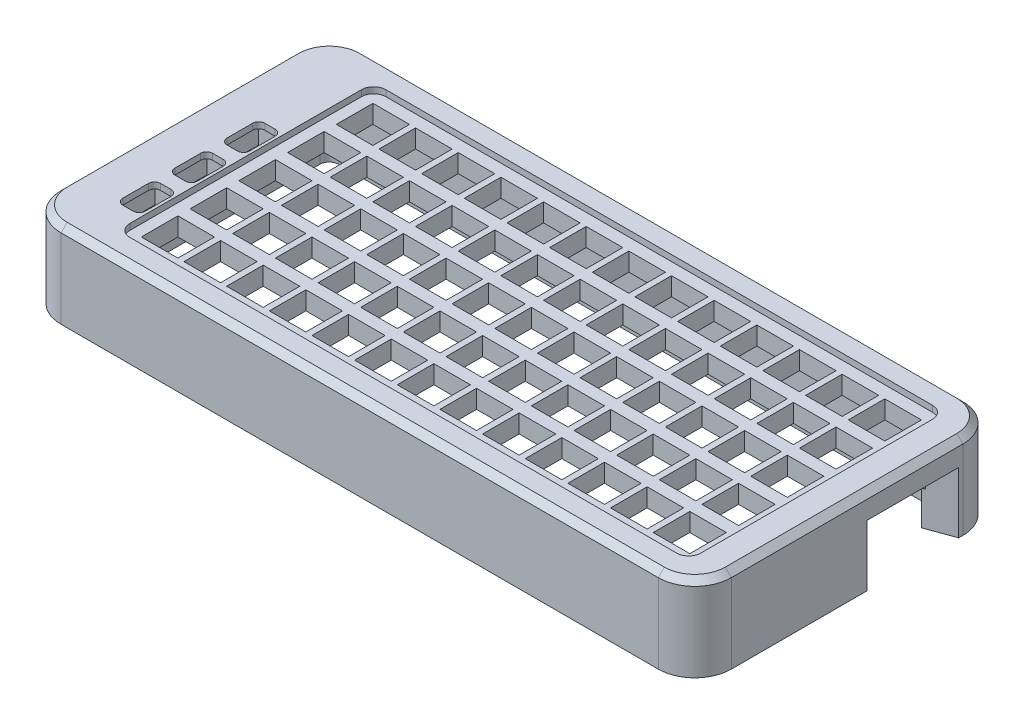
SolidWorks part; units mm, degrees
ref_plane "前视基准面" through (0, 0, 0) normal (0, 0, 1) x (1, 0, 0)
ref_plane "上视基准面" through (0, 0, 0) normal (0, 1, 0) x (1, 0, 0)
ref_plane "右视基准面" through (0, 0, 0) normal (1, 0, 0) x (0, 0, -1)
other "Configuration Table"
sketch "草图1" plane through (0, 0, 0) normal (0, 1, 0) x (1, 0, 0)
  line L1 (-55, -25) -> (55, -25)
  line L2 (-55, -25) -> (-55, 25)
  line L3 (-55, 25) -> (55, 25)
  line L4 (55, -25) -> (55, 25)
  line L5 (-55, -25) -> (55, 25) construction
  line L6 (-55, 25) -> (55, -25) construction
  point P0 (0, 0)
  dimension "D1" = 50
  dimension "D2" = 110
extrude "凸台-拉伸1" add sketch "草图1" along normal blind 3
sketch "草图2" plane through (0, 0, 0) normal (0, -1, 0) x (1, 0, 0)
  line L0 (46.3251, 14.2) -> (44.0251, 17.8) construction
  line L1 (48.1751, 11) -> (48.1751, 5)
  line L2 (48.1751, 19) -> (42.1751, 19)
  line L3 (48.1751, 19) -> (48.1751, 13)
  line L4 (48.1751, 13) -> (42.1751, 13)
  line L5 (42.1751, 19) -> (42.1751, 13)
  line L6 (48.1751, 19) -> (42.1751, 13) construction
  line L7 (48.1751, 13) -> (42.1751, 19) construction
  line L8 (48.1751, 5) -> (42.1751, 5)
  line L9 (42.1751, 11) -> (42.1751, 5)
  line L10 (48.1751, 11) -> (42.1751, 11)
  line L11 (48.1751, 3) -> (48.1751, -3)
  line L12 (48.1751, -3) -> (42.1751, -3)
  line L13 (42.1751, 3) -> (42.1751, -3)
  line L14 (48.1751, 3) -> (42.1751, 3)
  line L15 (48.1751, -5) -> (48.1751, -11)
  line L16 (48.1751, -11) -> (42.1751, -11)
  line L17 (42.1751, -5) -> (42.1751, -11)
  line L18 (48.1751, -5) -> (42.1751, -5)
  line L19 (48.1751, -13) -> (48.1751, -19)
  line L20 (48.1751, -19) -> (42.1751, -19)
  line L21 (42.1751, -13) -> (42.1751, -19)
  line L22 (48.1751, -13) -> (42.1751, -13)
  line L23 (41.1751, 11) -> (41.1751, 5)
  line L24 (41.1751, 5) -> (35.1751, 5)
  line L25 (35.1751, 11) -> (35.1751, 5)
  line L26 (41.1751, 11) -> (35.1751, 11)
  line L27 (41.1751, 3) -> (41.1751, -3)
  line L28 (41.1751, -3) -> (35.1751, -3)
  line L29 (35.1751, 3) -> (35.1751, -3)
  line L30 (41.1751, 3) -> (35.1751, 3)
  line L31 (41.1751, -5) -> (41.1751, -11)
  line L32 (41.1751, -11) -> (35.1751, -11)
  line L33 (35.1751, -5) -> (35.1751, -11)
  line L34 (41.1751, -5) -> (35.1751, -5)
  line L35 (41.1751, -13) -> (41.1751, -19)
  line L36 (41.1751, -19) -> (35.1751, -19)
  line L37 (35.1751, -13) -> (35.1751, -19)
  line L38 (41.1751, -13) -> (35.1751, -13)
  line L39 (34.1751, 11) -> (34.1751, 5)
  line L40 (34.1751, 5) -> (28.1751, 5)
  line L41 (28.1751, 11) -> (28.1751, 5)
  line L42 (34.1751, 11) -> (28.1751, 11)
  line L43 (34.1751, 3) -> (34.1751, -3)
  line L44 (34.1751, -3) -> (28.1751, -3)
  line L45 (28.1751, 3) -> (28.1751, -3)
  line L46 (34.1751, 3) -> (28.1751, 3)
  line L47 (34.1751, -5) -> (34.1751, -11)
  line L48 (34.1751, -11) -> (28.1751, -11)
  line L49 (28.1751, -5) -> (28.1751, -11)
  line L50 (34.1751, -5) -> (28.1751, -5)
  line L51 (34.1751, -13) -> (34.1751, -19)
  line L52 (34.1751, -19) -> (28.1751, -19)
  line L53 (28.1751, -13) -> (28.1751, -19)
  line L54 (34.1751, -13) -> (28.1751, -13)
  line L55 (27.1751, 11) -> (27.1751, 5)
  line L56 (27.1751, 5) -> (21.1751, 5)
  line L57 (21.1751, 11) -> (21.1751, 5)
  line L58 (27.1751, 11) -> (21.1751, 11)
  line L59 (27.1751, 3) -> (27.1751, -3)
  line L60 (27.1751, -3) -> (21.1751, -3)
  line L61 (21.1751, 3) -> (21.1751, -3)
  line L62 (27.1751, 3) -> (21.1751, 3)
  line L63 (27.1751, -5) -> (27.1751, -11)
  line L64 (27.1751, -11) -> (21.1751, -11)
  line L65 (21.1751, -5) -> (21.1751, -11)
  line L66 (27.1751, -5) -> (21.1751, -5)
  line L67 (27.1751, -13) -> (27.1751, -19)
  line L68 (27.1751, -19) -> (21.1751, -19)
  line L69 (21.1751, -13) -> (21.1751, -19)
  line L70 (27.1751, -13) -> (21.1751, -13)
  line L71 (20.1751, 11) -> (20.1751, 5)
  line L72 (20.1751, 5) -> (14.1751, 5)
  line L73 (14.1751, 11) -> (14.1751, 5)
  line L74 (20.1751, 11) -> (14.1751, 11)
  line L75 (20.1751, 3) -> (20.1751, -3)
  line L76 (20.1751, -3) -> (14.1751, -3)
  line L77 (14.1751, 3) -> (14.1751, -3)
  line L78 (20.1751, 3) -> (14.1751, 3)
  line L79 (20.1751, -5) -> (20.1751, -11)
  line L80 (20.1751, -11) -> (14.1751, -11)
  line L81 (14.1751, -5) -> (14.1751, -11)
  line L82 (20.1751, -5) -> (14.1751, -5)
  line L83 (20.1751, -13) -> (20.1751, -19)
  line L84 (20.1751, -19) -> (14.1751, -19)
  line L85 (14.1751, -13) -> (14.1751, -19)
  line L86 (20.1751, -13) -> (14.1751, -13)
  line L87 (13.1751, 11) -> (13.1751, 5)
  line L88 (13.1751, 5) -> (7.1751, 5)
  line L89 (7.1751, 11) -> (7.1751, 5)
  line L90 (13.1751, 11) -> (7.1751, 11)
  line L91 (13.1751, 3) -> (13.1751, -3)
  line L92 (13.1751, -3) -> (7.1751, -3)
  line L93 (7.1751, 3) -> (7.1751, -3)
  line L94 (13.1751, 3) -> (7.1751, 3)
  line L95 (13.1751, -5) -> (13.1751, -11)
  line L96 (13.1751, -11) -> (7.1751, -11)
  line L97 (7.1751, -5) -> (7.1751, -11)
  line L98 (13.1751, -5) -> (7.1751, -5)
  line L99 (13.1751, -13) -> (13.1751, -19)
  line L100 (13.1751, -19) -> (7.1751, -19)
  line L101 (7.1751, -13) -> (7.1751, -19)
  line L102 (13.1751, -13) -> (7.1751, -13)
  line L103 (6.1751, 11) -> (6.1751, 5)
  line L104 (6.1751, 5) -> (0.1751, 5)
  line L105 (0.1751, 11) -> (0.1751, 5)
  line L106 (6.1751, 11) -> (0.1751, 11)
  line L107 (6.1751, 3) -> (6.1751, -3)
  line L108 (6.1751, -3) -> (0.1751, -3)
  line L109 (0.1751, 3) -> (0.1751, -3)
  line L110 (6.1751, 3) -> (0.1751, 3)
  line L111 (6.1751, -5) -> (6.1751, -11)
  line L112 (6.1751, -11) -> (0.1751, -11)
  line L113 (0.1751, -5) -> (0.1751, -11)
  line L114 (6.1751, -5) -> (0.1751, -5)
  line L115 (6.1751, -13) -> (6.1751, -19)
  line L116 (6.1751, -19) -> (0.1751, -19)
  line L117 (0.1751, -13) -> (0.1751, -19)
  line L118 (6.1751, -13) -> (0.1751, -13)
  line L119 (-0.8249, 11) -> (-0.8249, 5)
  line L120 (-0.8249, 5) -> (-6.8249, 5)
  line L121 (-6.8249, 11) -> (-6.8249, 5)
  line L122 (-0.8249, 11) -> (-6.8249, 11)
  line L123 (-0.8249, 3) -> (-0.8249, -3)
  line L124 (-0.8249, -3) -> (-6.8249, -3)
  line L125 (-6.8249, 3) -> (-6.8249, -3)
  line L126 (-0.8249, 3) -> (-6.8249, 3)
  line L127 (-0.8249, -5) -> (-0.8249, -11)
  line L128 (-0.8249, -11) -> (-6.8249, -11)
  line L129 (-6.8249, -5) -> (-6.8249, -11)
  line L130 (-0.8249, -5) -> (-6.8249, -5)
  line L131 (-0.8249, -13) -> (-0.8249, -19)
  line L132 (-0.8249, -19) -> (-6.8249, -19)
  line L133 (-6.8249, -13) -> (-6.8249, -19)
  line L134 (-0.8249, -13) -> (-6.8249, -13)
  line L135 (-7.8249, 11) -> (-7.8249, 5)
  line L136 (-7.8249, 5) -> (-13.8249, 5)
  line L137 (-13.8249, 11) -> (-13.8249, 5)
  line L138 (-7.8249, 11) -> (-13.8249, 11)
  line L139 (-7.8249, 3) -> (-7.8249, -3)
  line L140 (-7.8249, -3) -> (-13.8249, -3)
  line L141 (-13.8249, 3) -> (-13.8249, -3)
  line L142 (-7.8249, 3) -> (-13.8249, 3)
  line L143 (-7.8249, -5) -> (-7.8249, -11)
  line L144 (-7.8249, -11) -> (-13.8249, -11)
  line L145 (-13.8249, -5) -> (-13.8249, -11)
  line L146 (-7.8249, -5) -> (-13.8249, -5)
  line L147 (-7.8249, -13) -> (-7.8249, -19)
  line L148 (-7.8249, -19) -> (-13.8249, -19)
  line L149 (-13.8249, -13) -> (-13.8249, -19)
  line L150 (-7.8249, -13) -> (-13.8249, -13)
  line L151 (-14.8249, 11) -> (-14.8249, 5)
  line L152 (-14.8249, 5) -> (-20.8249, 5)
  line L153 (-20.8249, 11) -> (-20.8249, 5)
  line L154 (-14.8249, 11) -> (-20.8249, 11)
  line L155 (-14.8249, 3) -> (-14.8249, -3)
  line L156 (-14.8249, -3) -> (-20.8249, -3)
  line L157 (-20.8249, 3) -> (-20.8249, -3)
  line L158 (-14.8249, 3) -> (-20.8249, 3)
  line L159 (-14.8249, -5) -> (-14.8249, -11)
  line L160 (-14.8249, -11) -> (-20.8249, -11)
  line L161 (-20.8249, -5) -> (-20.8249, -11)
  line L162 (-14.8249, -5) -> (-20.8249, -5)
  line L163 (-14.8249, -13) -> (-14.8249, -19)
  line L164 (-14.8249, -19) -> (-20.8249, -19)
  line L165 (-20.8249, -13) -> (-20.8249, -19)
  line L166 (-14.8249, -13) -> (-20.8249, -13)
  line L167 (-21.8249, 11) -> (-21.8249, 5)
  line L168 (-21.8249, 5) -> (-27.8249, 5)
  line L169 (-27.8249, 11) -> (-27.8249, 5)
  line L170 (-21.8249, 11) -> (-27.8249, 11)
  line L171 (-21.8249, 3) -> (-21.8249, -3)
  line L172 (-21.8249, -3) -> (-27.8249, -3)
  line L173 (-27.8249, 3) -> (-27.8249, -3)
  line L174 (-21.8249, 3) -> (-27.8249, 3)
  line L175 (-21.8249, -5) -> (-21.8249, -11)
  line L176 (-21.8249, -11) -> (-27.8249, -11)
  line L177 (-27.8249, -5) -> (-27.8249, -11)
  line L178 (-21.8249, -5) -> (-27.8249, -5)
  line L179 (-21.8249, -13) -> (-21.8249, -19)
  line L180 (-21.8249, -19) -> (-27.8249, -19)
  line L181 (-27.8249, -13) -> (-27.8249, -19)
  line L182 (-21.8249, -13) -> (-27.8249, -13)
  line L183 (-28.8249, 11) -> (-28.8249, 5)
  line L184 (-28.8249, 5) -> (-34.8249, 5)
  line L185 (-34.8249, 11) -> (-34.8249, 5)
  line L186 (-28.8249, 11) -> (-34.8249, 11)
  line L187 (-28.8249, 3) -> (-28.8249, -3)
  line L188 (-28.8249, -3) -> (-34.8249, -3)
  line L189 (-34.8249, 3) -> (-34.8249, -3)
  line L190 (-28.8249, 3) -> (-34.8249, 3)
  line L191 (-28.8249, -5) -> (-28.8249, -11)
  line L192 (-28.8249, -11) -> (-34.8249, -11)
  line L193 (-34.8249, -5) -> (-34.8249, -11)
  line L194 (-28.8249, -5) -> (-34.8249, -5)
  line L195 (-28.8249, -13) -> (-28.8249, -19)
  line L196 (-28.8249, -19) -> (-34.8249, -19)
  line L197 (-34.8249, -13) -> (-34.8249, -19)
  line L198 (-28.8249, -13) -> (-34.8249, -13)
  line L199 (-35.8249, 11) -> (-35.8249, 5)
  line L200 (-35.8249, 5) -> (-41.8249, 5)
  line L201 (-41.8249, 11) -> (-41.8249, 5)
  line L202 (-35.8249, 11) -> (-41.8249, 11)
  line L203 (-35.8249, 3) -> (-35.8249, -3)
  line L204 (-35.8249, -3) -> (-41.8249, -3)
  line L205 (-41.8249, 3) -> (-41.8249, -3)
  line L206 (-35.8249, 3) -> (-41.8249, 3)
  line L207 (-35.8249, -5) -> (-35.8249, -11)
  line L208 (-35.8249, -11) -> (-41.8249, -11)
  line L209 (-41.8249, -5) -> (-41.8249, -11)
  line L210 (-35.8249, -5) -> (-41.8249, -5)
  line L211 (-35.8249, -13) -> (-35.8249, -19)
  line L212 (-35.8249, -19) -> (-41.8249, -19)
  line L213 (-41.8249, -13) -> (-41.8249, -19)
  line L214 (-35.8249, -13) -> (-41.8249, -13)
  line L215 (41.1751, 19) -> (41.1751, 13)
  line L216 (41.1751, 13) -> (35.1751, 13)
  line L217 (35.1751, 19) -> (35.1751, 13)
  line L218 (41.1751, 19) -> (35.1751, 19)
  line L219 (34.1751, 19) -> (34.1751, 13)
  line L220 (34.1751, 13) -> (28.1751, 13)
  line L221 (28.1751, 19) -> (28.1751, 13)
  line L222 (34.1751, 19) -> (28.1751, 19)
  line L223 (27.1751, 19) -> (27.1751, 13)
  line L224 (27.1751, 13) -> (21.1751, 13)
  line L225 (21.1751, 19) -> (21.1751, 13)
  line L226 (27.1751, 19) -> (21.1751, 19)
  line L227 (20.1751, 19) -> (20.1751, 13)
  line L228 (20.1751, 13) -> (14.1751, 13)
  line L229 (14.1751, 19) -> (14.1751, 13)
  line L230 (20.1751, 19) -> (14.1751, 19)
  line L231 (13.1751, 19) -> (13.1751, 13)
  line L232 (13.1751, 13) -> (7.1751, 13)
  line L233 (7.1751, 19) -> (7.1751, 13)
  line L234 (13.1751, 19) -> (7.1751, 19)
  line L235 (6.1751, 19) -> (6.1751, 13)
  line L236 (6.1751, 13) -> (0.1751, 13)
  line L237 (0.1751, 19) -> (0.1751, 13)
  line L238 (6.1751, 19) -> (0.1751, 19)
  line L239 (-0.8249, 19) -> (-0.8249, 13)
  line L240 (-0.8249, 13) -> (-6.8249, 13)
  line L241 (-6.8249, 19) -> (-6.8249, 13)
  line L242 (-0.8249, 19) -> (-6.8249, 19)
  line L243 (-7.8249, 19) -> (-7.8249, 13)
  line L244 (-7.8249, 13) -> (-13.8249, 13)
  line L245 (-13.8249, 19) -> (-13.8249, 13)
  line L246 (-7.8249, 19) -> (-13.8249, 19)
  line L247 (-14.8249, 19) -> (-14.8249, 13)
  line L248 (-14.8249, 13) -> (-20.8249, 13)
  line L249 (-20.8249, 19) -> (-20.8249, 13)
  line L250 (-14.8249, 19) -> (-20.8249, 19)
  line L251 (-21.8249, 19) -> (-21.8249, 13)
  line L252 (-21.8249, 13) -> (-27.8249, 13)
  line L253 (-27.8249, 19) -> (-27.8249, 13)
  line L254 (-21.8249, 19) -> (-27.8249, 19)
  line L255 (-28.8249, 19) -> (-28.8249, 13)
  line L256 (-28.8249, 13) -> (-34.8249, 13)
  line L257 (-34.8249, 19) -> (-34.8249, 13)
  line L258 (-28.8249, 19) -> (-34.8249, 19)
  line L259 (-35.8249, 19) -> (-35.8249, 13)
  line L260 (-35.8249, 13) -> (-41.8249, 13)
  line L261 (-41.8249, 19) -> (-41.8249, 13)
  line L262 (-35.8249, 19) -> (-41.8249, 19)
  point P2 (45.1751, 16)
  dimension "D1" = 6
  dimension "D2" = 6
  dimension "D3" = 5
  dimension "D4" = 13
extrude "切除-拉伸1" cut sketch "草图2" against normal blind 10
sketch "草图3" plane through (0, 3, 0) normal (0, 1, 0) x (1, 0, 0)
  line L0 (-55, 25) -> (-55, -25) construction
  line L1 (-55, 25) -> (55, 25)
  line L2 (-55, 25) -> (-55, -25)
  line L3 (-55, -25) -> (55, -25)
  line L4 (55, 25) -> (55, -25)
  line L5 (55, 25) -> (-55, 25) construction
  line L6 (55, -25) -> (55, 25) construction
  line L7 (-55, -25) -> (55, -25) construction
  line L9 (-43.7, 21) -> (50, 21)
  line L10 (-43.7, 21) -> (-43.7, -21)
  line L11 (-43.7, -21) -> (50, -21)
  line L12 (50, 21) -> (50, -21)
  dimension "D1" = 4
  dimension "D2" = 4
  dimension "D3" = 5
  dimension "D4" = 42
  dimension "D5" = 11.3
extrude "凸台-拉伸2" add sketch "草图3" along normal blind 1
fillet "圆角1" radius 6 4 edges at (-55, 2, -25) (-55, 2, 25) (55, 2, 25) (55, 2, -25)
sketch "草图4" plane through (0, 0, 0) normal (0, -1, 0) x (1, 0, 0)
  line L0 (-45.3973, -4.764) -> (-46.6251, -1.636) construction
  line L1 (-45.3973, 3.786) -> (-46.6251, 6.914) construction
  line L2 (-45.1612, -0.1) -> (-46.8612, -0.1)
  line L3 (-44.1612, -1.1) -> (-44.1612, -5.3)
  line L4 (-45.1612, -6.3) -> (-46.8612, -6.3)
  line L5 (-47.8612, -1.1) -> (-47.8612, -5.3)
  line L6 (-44.1612, -0.1) -> (-47.8612, -6.3) construction
  line L7 (-44.1612, -6.3) -> (-47.8612, -0.1) construction
  line L8 (-44.1612, 7.45) -> (-44.1612, 3.25)
  line L9 (-45.1612, 8.45) -> (-46.8612, 8.45)
  line L10 (-47.8612, 7.45) -> (-47.8612, 3.25)
  line L11 (-45.1612, 2.25) -> (-46.8612, 2.25)
  line L12 (-45.3973, 12.336) -> (-46.6251, 15.464) construction
  line L13 (-44.1612, 16) -> (-44.1612, 11.8)
  line L14 (-45.1612, 17) -> (-46.8612, 17)
  line L15 (-47.8612, 16) -> (-47.8612, 11.8)
  line L16 (-45.1612, 10.8) -> (-46.8612, 10.8)
  arc A0 (-46.8612, 17) -> (-47.8612, 16) centre (-46.8612, 16) ccw
  arc A1 (-44.1612, 11.8) -> (-45.1612, 10.8) centre (-45.1612, 11.8) cw
  arc A2 (-44.1612, 16) -> (-45.1612, 17) centre (-45.1612, 16) ccw
  arc A3 (-47.8612, 11.8) -> (-46.8612, 10.8) centre (-46.8612, 11.8) ccw
  arc A4 (-46.8612, 8.45) -> (-47.8612, 7.45) centre (-46.8612, 7.45) ccw
  arc A5 (-44.1612, 3.25) -> (-45.1612, 2.25) centre (-45.1612, 3.25) cw
  arc A6 (-44.1612, 7.45) -> (-45.1612, 8.45) centre (-45.1612, 7.45) ccw
  arc A7 (-47.8612, 3.25) -> (-46.8612, 2.25) centre (-46.8612, 3.25) ccw
  arc A8 (-46.8612, -0.1) -> (-47.8612, -1.1) centre (-46.8612, -1.1) ccw
  arc A9 (-44.1612, -5.3) -> (-45.1612, -6.3) centre (-45.1612, -5.3) cw
  arc A10 (-45.1612, -0.1) -> (-44.1612, -1.1) centre (-45.1612, -1.1) cw
  arc A11 (-46.8612, -6.3) -> (-47.8612, -5.3) centre (-46.8612, -5.3) cw
  point P2 (-46.0112, -3.2)
  point P47 (-46.6251, -1.636)
  point P48 (0, 0)
  point P49 (-45.3973, -4.764)
  point P50 (-46.0112, -3.2)
  dimension "D4" = 1
  dimension "D1" = 3.7
  dimension "D2" = 6.2
  dimension "D5" = 3.7
  dimension "D6" = 1.7
  dimension "D7" = 6.2
  dimension "D3" = 3
extrude "切除-拉伸2" cut sketch "草图4" against normal blind 6
sketch "草图5" plane through (0, 0, 0) normal (0, -1, 0) x (1, 0, 0)
  line L0 (-46.0112, -6.3) -> (-46.0112, -0.1) construction
  line L1 (-46.8612, -6.3) -> (-45.1612, -6.3) construction
  line L2 (-45.1612, -0.1) -> (-46.8612, -0.1) construction
  line L3 (-43.7612, 8.8) -> (-43.7612, 1.8)
  line L4 (-43.7612, 0.3) -> (-48.2612, 0.3)
  line L5 (-43.7612, 0.3) -> (-43.7612, -6.7)
  line L6 (-43.7612, -6.7) -> (-48.2612, -6.7)
  line L7 (-48.2612, 0.3) -> (-48.2612, -6.7)
  line L8 (-43.7612, 0.3) -> (-48.2612, -6.7) construction
  line L9 (-43.7612, -6.7) -> (-48.2612, 0.3) construction
  line L10 (-43.7612, 8.8) -> (-48.2612, 8.8)
  line L11 (-48.2612, 8.8) -> (-48.2612, 1.8)
  line L12 (-43.7612, 1.8) -> (-48.2612, 1.8)
  line L13 (-43.7612, 17.3) -> (-43.7612, 10.3)
  line L14 (-43.7612, 17.3) -> (-48.2612, 17.3)
  line L15 (-48.2612, 17.3) -> (-48.2612, 10.3)
  line L16 (-43.7612, 10.3) -> (-48.2612, 10.3)
  point P6 (-46.0112, -3.2)
  dimension "D1" = 7
  dimension "D2" = 4.5
  dimension "D3" = 3
extrude "切除-拉伸3" cut sketch "草图5" against normal blind 3
fillet "圆角2" radius 2 4 edges at (50, 3.5, 21) (50, 3.5, -21) (-43.7, 3.5, -21) (-43.7, 3.5, 21)
chamfer "倒角1" distance 1 angle 45 8 edges at (53.2426, 4, -23.2426) (0, 4, -25) (55, 4, 0) (-53.2426, 4, -23.2426) (53.2426, 4, 23.2426) (-55, 4, 0) (0, 4, 25) (-53.2426, 4, 23.2426)
sketch "草图6" plane through (0, 0, 0) normal (0, -1, 0) x (1, 0, 0)
  line L6 (-55, 19) -> (-55, -19)
  line L7 (-49, -25) -> (49, -25)
  line L8 (-55, 19) -> (-55, -19)
  line L9 (-49, -25) -> (49, -25)
  line L10 (55, 19) -> (55, -19)
  line L11 (55, 19) -> (55, -19)
  line L13 (50.5, 19) -> (50.5, -19)
  line L14 (49, 25) -> (-49, 25)
  line L15 (49, 25) -> (-49, 25)
  line L16 (49, 20.5) -> (-49, 20.5)
  line L17 (-50.5, 19) -> (-50.5, -19)
  line L18 (-49, -20.5) -> (49, -20.5)
  arc A8 (-55, -19) -> (-49, -25) centre (-49, -19) ccw
  arc A9 (49, -25) -> (55, -19) centre (49, -19) ccw
  arc A10 (-55, -19) -> (-49, -25) centre (-49, -19) ccw
  arc A11 (49, -25) -> (55, -19) centre (49, -19) ccw
  arc A14 (49, -20.5) -> (50.5, -19) centre (49, -19) ccw
  arc A15 (50.5, 19) -> (49, 20.5) centre (49, 19) ccw
  arc A16 (-49, 25) -> (-55, 19) centre (-49, 19) ccw
  arc A17 (55, 19) -> (49, 25) centre (49, 19) ccw
  arc A18 (-49, 25) -> (-55, 19) centre (-49, 19) ccw
  arc A19 (55, 19) -> (49, 25) centre (49, 19) ccw
  arc A20 (-49, 20.5) -> (-50.5, 19) centre (-49, 19) ccw
  arc A21 (-50.5, -19) -> (-49, -20.5) centre (-49, -19) ccw
  dimension "D1" = 0
  dimension "D2" = 0
  dimension "D3" = 0
  dimension "D4" = 4.5
extrude "凸台-拉伸3" add sketch "草图6" along normal blind 10
sketch "草图8" plane through (-50.5, 0, 0) normal (1, 0, 0) x (0, 0, -1)
  line L0 (15.184, -3.8) -> (8.184, -3.8) construction
  line L1 (14.6841, -3.8) -> (8.6839, -3.8) construction
  line L2 (14.6841, -5.5485) -> (8.6839, -5.5485)
  line L3 (14.6841, -2.0515) -> (8.6839, -2.0515)
  line L4 (-19, 3) -> (19, 3) construction
  arc A0 (14.6841, -5.5485) -> (14.6841, -2.0515) centre (14.6841, -3.8) ccw
  arc A1 (8.6839, -2.0515) -> (8.6839, -5.5485) centre (8.6839, -3.8) ccw
  point P4 (11.684, -3.8)
  dimension "D1" = 6.8
extrude "切除-拉伸4" cut sketch "草图8" against normal blind 7
sketch "草图9" plane through (-55, 0, 0) normal (-1, 0, 0) x (0, 0, 1)
  line L0 (-15.0883, -3.8575) -> (-8.1531, -3.8575) construction
  line L1 (-15.0883, -0.0301) -> (-8.1531, -0.0301)
  line L4 (-15.0883, -7.685) -> (-8.1531, -7.685)
  line L5 (-14.6841, -2.0515) -> (-8.6839, -2.0515) construction
  arc A6 (-15.0883, -0.0301) -> (-15.0883, -7.685) centre (-15.0883, -3.8575) ccw
  arc A7 (-8.1531, -7.685) -> (-8.1531, -0.0301) centre (-8.1531, -3.8575) ccw
  point P2 (-11.6207, -3.8575)
  point P7 (0, 0)
  point P8 (-11.684, -3.2801)
  point P11 (0, 0)
  point P12 (-11.684, -3.2801)
  point P13 (0, 0)
  point P14 (-11.6207, -3.8575)
  dimension "D3" = 3.8275
  dimension "D2" = 2.0215
extrude "切除-拉伸5" cut sketch "草图9" against normal blind 3.5
sketch "草图10" plane through (50.5, 0, 0) normal (-1, 0, 0) x (0, 0, 1)
  line L1 (-4.7442, -1.4441) -> (-16.8485, -1.4441)
  line L2 (-4.7442, -1.4441) -> (-4.7442, -4.3565)
  line L3 (-4.7442, -4.3565) -> (-16.8485, -4.3565)
  line L4 (-16.8485, -1.4441) -> (-16.8485, -4.3565)
extrude "切除-拉伸6" cut sketch "草图10" against normal blind 6.5
chamfer "倒角2" distance 4 angle 20 1 edges at (55, -1.4441, -10.7963)
chamfer "倒角4" distance 4 angle 20 1 edges at (55, -2.1724, -4.7442)
chamfer "倒角5" distance 4 angle 20 1 edges at (55, -2.1724, -16.8485)
sketch "草图11" plane through (0, -10, 0) normal (0, -1, 0) x (1, 0, 0)
  line L0 (-49, -25) -> (49, -25) construction
  line L2 (0, 0) -> (50000, 0) construction
  circle A0 centre (0, -22.7) radius 1.55
  circle A1 centre (20, -22.7) radius 1.55
  circle A2 centre (40, -22.7) radius 1.55
  circle A3 centre (-20, -22.7) radius 1.55
  circle A4 centre (-40, -22.7) radius 1.55
  circle A5 centre (-40, 22.7) radius 1.55
  circle A6 centre (-20, 22.7) radius 1.55
  circle A7 centre (40, 22.7) radius 1.55
  circle A8 centre (20, 22.7) radius 1.55
  circle A9 centre (0, 22.7) radius 1.55
  dimension "D1" = 3.1
  dimension "D3" = 3
  dimension "D2" = 2.3
  dimension "D4" = 3
extrude "切除-拉伸7" cut sketch "草图11" against normal blind 2
sketch "草图14" plane through (0, -4.3565, 0) normal (0, 1, 0) x (1, 0, 0)
  line L0 (55, 18.3044) -> (55, 3.2883)
  line L1 (55, 18.3044) -> (55, 3.2883) construction
  line L2 (55, 19) -> (55, -19) construction
  line L3 (51, 4.7442) -> (55, 3.2883) construction
  line L4 (55, 3.2883) -> (53.8098, 3.7215)
  line L5 (53.8098, 3.7215) -> (49.1767, 5.4078)
  line L6 (49.1767, 5.4078) -> (49.1767, 16.1848)
  line L7 (55, 18.3044) -> (53.8098, 17.8712)
  line L8 (51, 16.8485) -> (55, 18.3044) construction
  line L9 (53.8098, 17.8712) -> (49.1767, 16.1848)
extrude "切除-拉伸8" cut sketch "草图14" against normal blind 10
